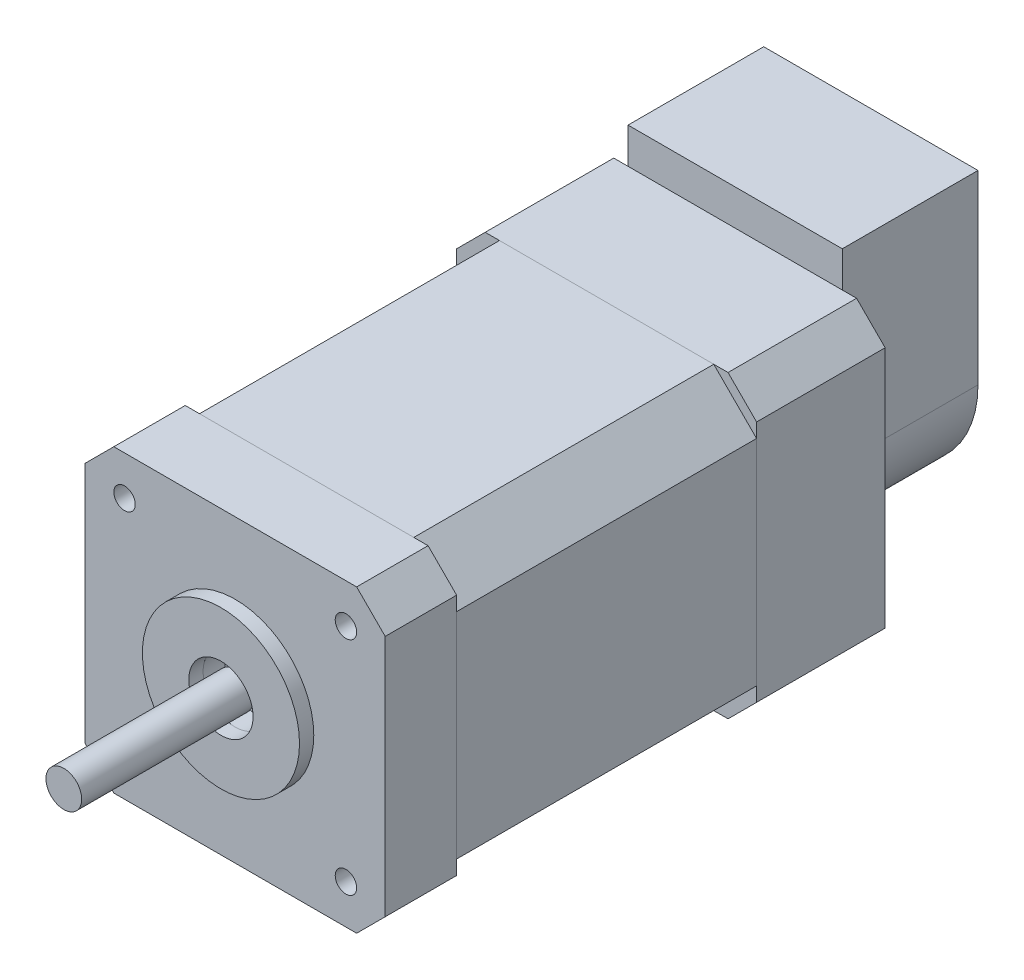
SolidWorks part; units mm, degrees
material "AISI 304"
ref_plane "前基準面" through (0, 0, 0) normal (0, 0, 1) x (1, 0, 0)
ref_plane "上基準面" through (0, 0, 0) normal (0, 1, 0) x (1, 0, 0)
ref_plane "右基準面" through (0, 0, 0) normal (1, 0, 0) x (0, 0, -1)
sketch "草圖1" plane through (0, 0, 0) normal (0, 0, 1) x (1, 0, 0)
  line L1 (-21, -21) -> (21, -21)
  line L2 (-21, -21) -> (-21, 21)
  line L3 (-21, 21) -> (21, 21)
  line L4 (21, -21) -> (21, 21)
  line L5 (-21, -21) -> (21, 21) construction
  line L6 (-21, 21) -> (21, -21) construction
  point P0 (0, 0)
  dimension "D1" = 42
  dimension "D2" = 42
extrude "填料-伸長1" add sketch "草圖1" along normal mid plane 42
chamfer "導角1" distance 6 angle 45 4 edges at (21, -21, 0) (-21, -21, 0) (-21, 21, 0) (21, 21, 0)
sketch "草圖15" plane through (0, 0, 21) normal (0, 0, 1) x (1, 0, 0)
  line L0 (15, 21) -> (-15, 21) construction
  line L1 (-21, -21) -> (21, -21)
  line L2 (-21, -21) -> (-21, 21)
  line L3 (-21, 21) -> (21, 21)
  line L4 (21, -21) -> (21, 21)
  line L5 (-21, -21) -> (21, 21) construction
  line L6 (-21, 21) -> (21, -21) construction
  line L7 (21, -15) -> (21, 15) construction
  point P0 (0, 0)
extrude "填料-伸長11" add sketch "草圖15" along normal blind 10 separate body
sketch "草圖16" plane through (0, 0, -21) normal (0, 0, -1) x (-1, 0, 0)
  line L1 (-21, -21) -> (21, -21)
  line L2 (-21, -21) -> (-21, 21)
  line L3 (-21, 21) -> (21, 21)
  line L4 (21, -21) -> (21, 21)
  line L5 (-21, -21) -> (21, 21) construction
  line L6 (-21, 21) -> (21, -21) construction
  line L8 (-15, 21) -> (15, 21) construction
  line L9 (21, 15) -> (21, -15) construction
  point P0 (0, 0)
extrude "填料-伸長12" add sketch "草圖16" along normal blind 8.5 separate body
sketch "草圖17" plane through (0, 0, -29.5) normal (0, 0, 1) x (1, 0, 0)
  line L0 (-21, 21) -> (21, 21) construction
  line L1 (-21, -21) -> (21, -21)
  line L2 (-21, -21) -> (-21, 21)
  line L3 (-21, 21) -> (21, 21)
  line L4 (21, -21) -> (21, 21)
  line L5 (-21, -21) -> (21, 21) construction
  line L6 (-21, 21) -> (21, -21) construction
  line L7 (21, 21) -> (21, -21) construction
  point P0 (0, 0)
extrude "填料-伸長13" add sketch "草圖17" against normal blind 9.5
chamfer "導角2" distance 4 angle 45 4 edges at (-21, -21, 26) (21, -21, 26) (21, 21, 26) (-21, 21, 26)
chamfer "導角3" distance 4 angle 45 4 edges at (-21, -21, -30) (21, -21, -30) (-21, 21, -30) (21, 21, -30)
sketch "草圖2" plane through (0, 0, 31) normal (0, 0, 1) x (1, 0, 0)
  circle A0 centre (0, 0) radius 11
  dimension "D1" = 22
extrude "填料-伸長2" add sketch "草圖2" along normal blind 2
sketch "草圖3" plane through (0, 0, 33) normal (0, 0, 1) x (1, 0, 0)
  circle A0 centre (0, 0) radius 4.5
  dimension "D1" = 9
extrude "除料-伸長1" cut sketch "草圖3" along direction (0, 0, -1) on the side against the normal blind 5
sketch "草圖6" plane through (0, 0, 31) normal (0, 0, 1) x (1, 0, 0)
  circle A0 centre (0, 0) radius 2.5
  dimension "D1" = 5
extrude "填料-伸長9" add sketch "草圖6" along direction (0, 0, 1) on the side of the normal offset from surface (24 mm away) 22 separate body
sketch "草圖9" plane through (0, 0, -39) normal (0, 0, -1) x (-1, 0, 0)
  line L0 (-15, 0) -> (-15, 26)
  line L1 (-15, 26) -> (15, 26)
  line L2 (15, 26) -> (15, 0)
  arc A0 (15, 0) -> (-15, 0) centre (0, 0) cw
  point P6 (0, -15)
  dimension "D1" = 15
  dimension "D2" = 41
extrude "填料-伸長10" add sketch "草圖9" along normal blind 19 separate body
sketch "草圖8" plane through (0, 0, 31) normal (0, 0, 1) x (1, 0, 0)
  line L0 (0, 0) -> (0, 15.5) construction
  line L1 (0, 15.5) -> (-15.5, 15.5) construction
  circle A0 centre (-15.5, 15.5) radius 1.5
  dimension "D3" = 3
  dimension "D1" = 15.5
  dimension "D2" = 15.5
extrude "除料-伸長3" cut sketch "草圖8" against normal blind 4.5
sketch "草圖11" plane through (0, 0, 55) normal (0, 0, 1) x (1, 0, 0)
  line L0 (-2, 1.5) -> (2, 1.5)
  circle A0 centre (0, 0) radius 2.5 construction
  arc A1 (2, 1.5) -> (-2, 1.5) centre (0, 0) ccw
  point P5 (0, 1.5)
  point P6 (0, 2.5)
  dimension "D1" = 1
extrude "除料-伸長4" [suppressed] cut sketch "草圖11" against normal blind 18
pattern_circular "環狀複製排列1" count 4 over 360 about axis through (0, 0, 0) along (0, 0, 1) of "除料-伸長3"
